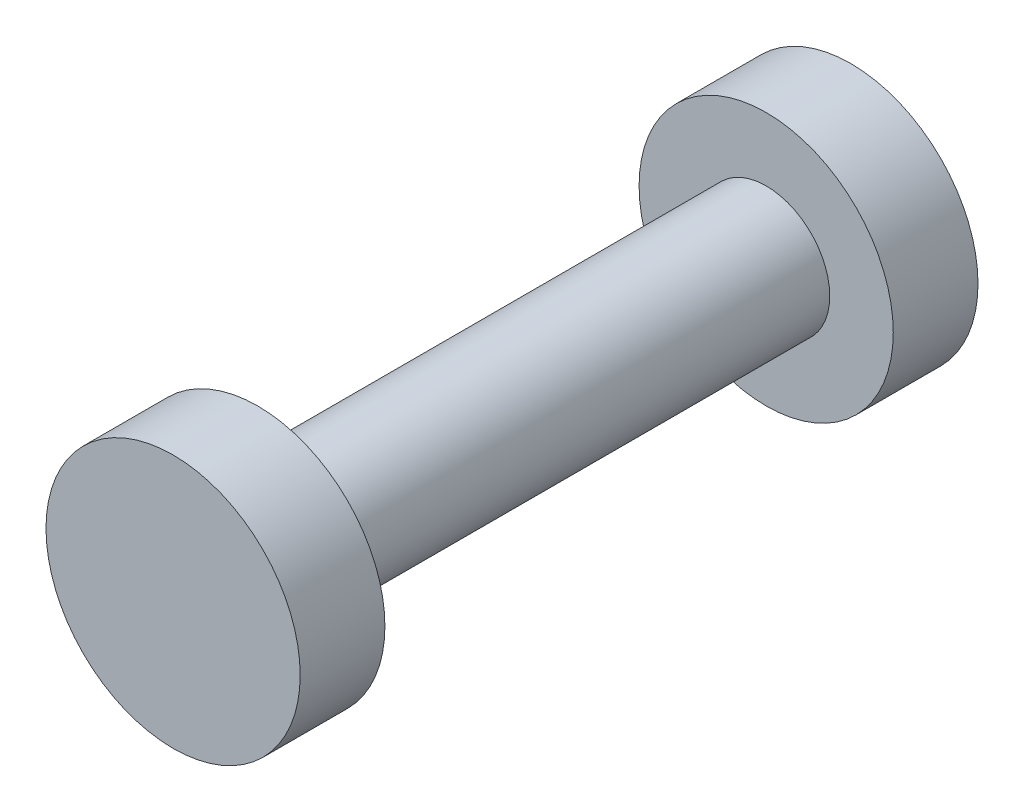
SolidWorks part; units mm, degrees
ref_plane "Front" through (0, 0, 0) normal (0, 0, 1) x (1, 0, 0)
ref_plane "Top" through (0, 0, 0) normal (0, 1, 0) x (1, 0, 0)
ref_plane "Right" through (0, 0, 0) normal (1, 0, 0) x (0, 0, -1)
sketch "Sketch1" plane through (0, 0, 0) normal (0, 0, 1) x (1, 0, 0)
  circle A0 centre (0, 0) radius 1.905
  dimension "D1" = 3.81
extrude "Boss-Extrude1" add sketch "Sketch1" along normal blind 15.24
ref_plane "Plane1" through (0, 0, 7.62) normal (0, 0, 1) x (1, 0, 0)
sketch "Sketch3" plane through (0, 0, 15.24) normal (0, 0, 1) x (1, 0, 0)
  circle A0 centre (0, 0) radius 3.81
  dimension "D1" = 7.62
extrude "Boss-Extrude2" add sketch "Sketch3" along normal blind 2.54
mirror "Mirror1" about plane through (0, 0, 7.62) normal (0, 0, 1) of "Boss-Extrude2"
